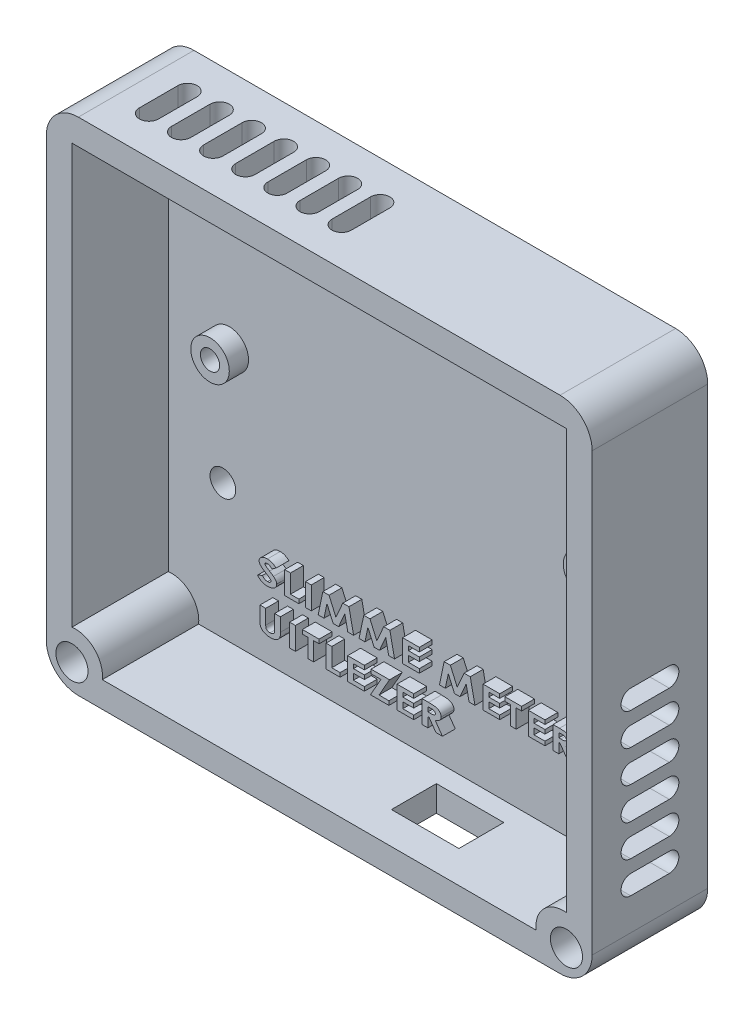
SolidWorks part; units mm, degrees
ref_plane "Front Plane" through (0, 0, 0) normal (0, 0, 1) x (1, 0, 0)
ref_plane "Top Plane" through (0, 0, 0) normal (0, 1, 0) x (1, 0, 0)
ref_plane "Right Plane" through (0, 0, 0) normal (1, 0, 0) x (0, 0, -1)
sketch "Sketch1" plane through (0, 0, 0) normal (0, 0, 1) x (1, 0, 0)
  line L0 (32.5, 30) -> (32.5, 0) construction
  line L1 (3, 0) -> (62, 0)
  line L2 (0, 3) -> (0, 27)
  line L3 (3, 30) -> (62, 30)
  line L4 (65, 3) -> (65, 27)
  line L5 (32.5, 15) -> (65, 15) construction
  line L7 (-10, 38) -> (75, 38)
  line L8 (-10, 38) -> (-10, -40)
  line L9 (-10, -40) -> (75, -40)
  line L10 (75, 38) -> (75, -40)
  circle A0 centre (3.5, 26.5) radius 1.5
  circle A1 centre (61.5, 26.5) radius 1.5
  circle A2 centre (61.5, 3.5) radius 1.5
  circle A3 centre (3.5, 3.5) radius 1.5
  arc A4 (62, 30) -> (65, 27) centre (62, 27) cw
  arc A5 (65, 3) -> (62, 0) centre (62, 3) cw
  arc A6 (3, 0) -> (0, 3) centre (3, 3) cw
  arc A7 (0, 27) -> (3, 30) centre (3, 27) cw
  point P19 (65, 30)
  point P22 (65, 0)
  point P25 (0, 0)
  point P28 (0, 30)
  dimension "D3" = 3.5
  dimension "D4" = 3
  dimension "D6" = 3
  dimension "D1" = 65
  dimension "D2" = 30
  dimension "D5" = 3.5
  dimension "D7" = 85
  dimension "D8" = 8
  dimension "D9" = 10
  dimension "D10" = 40
extrude "Base Plate" add sketch "Sketch1" along normal blind 3 contours L10 L7 L8 L9 L2 A7 L3 A4 L4 A5 L1 A6 | A7 L2 A6 L1 A5 L4 A4 L3 A1 A0 A2 A3
sketch "Sketch2" plane through (0, 0, 3) normal (0, 0, 1) x (1, 0, 0)
  line L0 (32.5, 38) -> (32.5, -40) construction
  line L1 (-10, 38) -> (75, 38) construction
  line L2 (-10, -40) -> (75, -40) construction
  circle A0 centre (3.5, 26.5) radius 1.5
  circle A1 centre (61.5, 26.5) radius 1.5
  circle A2 centre (61.5, 3.5) radius 1.5
  circle A3 centre (3.5, 3.5) radius 1.5
  circle A4 centre (3.5, 26.5) radius 3
  circle A5 centre (3.5, 3.5) radius 3
  circle A6 centre (61.5, 26.5) radius 3
  circle A7 centre (61.5, 3.5) radius 3
  dimension "D1" = 3
  dimension "D2" = 3
  dimension "D3" = 3
  dimension "D4" = 3
  dimension "D5" = 6
  dimension "D6" = 6
  dimension "D7" = 6
  dimension "D8" = 6
extrude "Pi Zero Staanders" add sketch "Sketch2" along normal blind 3
sketch "Sketch3" plane through (0, 0, 3) normal (0, 0, 1) x (1, 0, 0)
  line L1 (-10, 38) -> (75, 38)
  line L2 (-10, 38) -> (-10, -40)
  line L3 (-10, -40) -> (75, -40)
  line L4 (75, 38) -> (75, -40)
  line L5 (-6, 34) -> (71, 34)
  line L6 (-6, 34) -> (-6, -36)
  line L7 (-6, -36) -> (71, -36)
  line L8 (71, 34) -> (71, -36)
  dimension "D1" = 4
  dimension "D2" = 4
  dimension "D3" = 4
  dimension "D4" = 4
extrude "Base Walls" add sketch "Sketch3" along normal blind 15
sketch "Sketch5" plane through (0, -40, 0) normal (0, -1, 0) x (1, 0, 0)
  line L0 (-10, 0) -> (75, 0) construction
  line L1 (38.75, 13) -> (49.25, 13)
  line L2 (38.75, 13) -> (38.75, 6)
  line L3 (38.75, 6) -> (49.25, 6)
  line L4 (49.25, 13) -> (49.25, 6)
  line L6 (44, 13) -> (44, 6) construction
  line L7 (-10, 18) -> (-10, 0) construction
  dimension "D1" = 10.5
  dimension "D2" = 7
  dimension "D3" = 6
  dimension "D4" = 54
extrude "USB Power uitsnede" cut sketch "Sketch5" against normal blind 4 contours L2 L1 L4 L3
fillet "Fillet1" radius 5 1 edges at (75, 38, 9)
fillet "Fillet2" radius 5 1 edges at (-10, 38, 9)
fillet "Fillet3" radius 5 1 edges at (-10, -40, 9)
fillet "Fillet4" radius 5 1 edges at (75, -40, 9)
sketch "Sketch9" plane through (75, 0, 0) normal (1, 0, 0) x (0, 0, -1)
  line L0 (-9, -40) -> (-9, 38) construction
  line L1 (0, -40) -> (-18, -40) construction
  line L2 (-18, 38) -> (0, 38) construction
  line L3 (-12, -28.5) -> (-6, -28.5) construction
  line L4 (-12, -27) -> (-6, -27)
  line L5 (-12, -30) -> (-6, -30)
  line L6 (-18, -35) -> (-18, 33) construction
  line L9 (-12, -23.5) -> (-6, -23.5) construction
  line L12 (-12, -22) -> (-6, -22)
  line L15 (-12, -25) -> (-6, -25)
  line L18 (-12, -18.5) -> (-6, -18.5) construction
  line L19 (-12, -17) -> (-6, -17)
  line L20 (-12, -20) -> (-6, -20)
  line L21 (-12, -13.5) -> (-6, -13.5) construction
  line L22 (-12, -12) -> (-6, -12)
  line L23 (-12, -15) -> (-6, -15)
  line L24 (-12, -8.5) -> (-6, -8.5) construction
  line L25 (-12, -7) -> (-6, -7)
  line L26 (-12, -10) -> (-6, -10)
  line L27 (-12, -3.5) -> (-6, -3.5) construction
  line L28 (-12, -2) -> (-6, -2)
  line L29 (-12, -5) -> (-6, -5)
  arc A0 (-12, -27) -> (-12, -30) centre (-12, -28.5) ccw
  arc A1 (-6, -30) -> (-6, -27) centre (-6, -28.5) ccw
  arc A10 (-12, -22) -> (-12, -25) centre (-12, -23.5) ccw
  arc A11 (-6, -25) -> (-6, -22) centre (-6, -23.5) ccw
  arc A12 (-12, -17) -> (-12, -20) centre (-12, -18.5) ccw
  arc A13 (-6, -20) -> (-6, -17) centre (-6, -18.5) ccw
  arc A14 (-12, -12) -> (-12, -15) centre (-12, -13.5) ccw
  arc A15 (-6, -15) -> (-6, -12) centre (-6, -13.5) ccw
  arc A16 (-12, -7) -> (-12, -10) centre (-12, -8.5) ccw
  arc A17 (-6, -10) -> (-6, -7) centre (-6, -8.5) ccw
  arc A18 (-12, -2) -> (-12, -5) centre (-12, -3.5) ccw
  arc A19 (-6, -5) -> (-6, -2) centre (-6, -3.5) ccw
  point P8 (-9, -28.5)
  point P18 (-9, -23.5)
  point P25 (-9, -18.5)
  point P32 (-9, -13.5)
  point P39 (-9, -8.5)
  point P46 (-9, -3.5)
  dimension "D3" = 9
  dimension "D1" = 3
  dimension "D2" = 10
  dimension "D5" = 6
  dimension "D4" = 6
extrude "Lucht ventilatie Rechts" cut sketch "Sketch9" against normal blind 4 contours L25 A17 L26 A16 | L22 A15 L23 A14 | L19 A13 L20 A12 | L12 A11 L15 A10 | L5 A1 L4 A0 | L28 A19 L29 A18
sketch "Sketch10" plane through (0, 0, 3) normal (0, 0, 1) x (1, 0, 0)
  line L0 (32.5, 38) -> (32.5, -40) construction
  line L1 (70, 38) -> (-5, 38) construction
  line L2 (-5, -40) -> (70, -40) construction
  line L3 (32.5, -1) -> (-10, -1) construction
  line L4 (-10, 33) -> (-10, -35) construction
  circle A0 centre (2.5, -15.0716) radius 2
  circle A1 centre (62.5, -15.0716) radius 2
  dimension "D2" = 4
  dimension "D3" = 4
  dimension "D4" = 30
  dimension "D5" = 30
extrude "Holes for screw" cut sketch "Sketch10" against normal through all
sketch "Sketch11" plane through (0, 38, 0) normal (0, 1, 0) x (1, 0, 0)
  line L0 (-10, -9) -> (75, -9) construction
  line L1 (-10, -18) -> (-10, 0) construction
  line L2 (75, 0) -> (75, -18) construction
  line L3 (0, -12) -> (0, -6) construction
  line L4 (-1.5, -12) -> (-1.5, -6)
  line L5 (1.5, -12) -> (1.5, -6)
  line L6 (6.5, -12) -> (6.5, -6)
  line L9 (3.5, -12) -> (3.5, -6)
  line L12 (5, -12) -> (5, -6) construction
  line L15 (11.5, -12) -> (11.5, -6)
  line L18 (8.5, -12) -> (8.5, -6)
  line L21 (10, -12) -> (10, -6) construction
  line L24 (16.5, -12) -> (16.5, -6)
  line L27 (13.5, -12) -> (13.5, -6)
  line L30 (15, -12) -> (15, -6) construction
  line L33 (21.5, -12) -> (21.5, -6)
  line L36 (18.5, -12) -> (18.5, -6)
  line L39 (20, -12) -> (20, -6) construction
  line L42 (26.5, -12) -> (26.5, -6)
  line L45 (23.5, -12) -> (23.5, -6)
  line L48 (25, -12) -> (25, -6) construction
  line L49 (31.5, -12) -> (31.5, -6)
  line L50 (28.5, -12) -> (28.5, -6)
  line L51 (30, -12) -> (30, -6) construction
  arc A0 (-1.5, -12) -> (1.5, -12) centre (0, -12) ccw
  arc A1 (1.5, -6) -> (-1.5, -6) centre (0, -6) ccw
  arc A30 (3.5, -12) -> (6.5, -12) centre (5, -12) ccw
  arc A31 (6.5, -6) -> (3.5, -6) centre (5, -6) ccw
  arc A32 (8.5, -12) -> (11.5, -12) centre (10, -12) ccw
  arc A33 (11.5, -6) -> (8.5, -6) centre (10, -6) ccw
  arc A34 (13.5, -12) -> (16.5, -12) centre (15, -12) ccw
  arc A35 (16.5, -6) -> (13.5, -6) centre (15, -6) ccw
  arc A36 (18.5, -12) -> (21.5, -12) centre (20, -12) ccw
  arc A37 (21.5, -6) -> (18.5, -6) centre (20, -6) ccw
  arc A38 (23.5, -12) -> (26.5, -12) centre (25, -12) ccw
  arc A39 (26.5, -6) -> (23.5, -6) centre (25, -6) ccw
  arc A40 (28.5, -12) -> (31.5, -12) centre (30, -12) ccw
  arc A41 (31.5, -6) -> (28.5, -6) centre (30, -6) ccw
  point P8 (0, -9)
  point P17 (5, -9)
  point P24 (10, -9)
  point P31 (15, -9)
  point P38 (20, -9)
  point P45 (25, -9)
  point P52 (30, -9)
  dimension "D2" = 6
  dimension "D1" = 3
  dimension "D3" = 10
  dimension "D4" = 7
extrude "Cool holes" cut sketch "Sketch11" against normal blind 4
sketch "Sketch15" plane through (0, 0, 3) normal (0, 0, 1) x (1, 0, 0)
  line L0 (-10, 33) -> (-10, -35) construction
  line L1 (-5, -40) -> (70, -40) construction
  line L2 (32.5, 38) -> (32.5, -40) construction
  line L4 (70, 38) -> (-5, 38) construction
  circle A0 centre (-5.5, -35.5) radius 4.25
  circle A2 centre (-5.5, -35.5) radius 1.475
  circle A3 centre (70.5, -35.5) radius 1.475
  circle A4 centre (70.5, -35.5) radius 4.25
  dimension "D3" = 8.5
  dimension "D4" = 2.95
  dimension "D1" = 4.5
  dimension "D2" = 4.5
extrude "Screw Holes" add sketch "Sketch15" along normal through all contours A0 | A2 | A4 | A3
sketch "Sketch17" plane through (0, 0, 3) normal (0, 0, 1) x (1, 0, 0)
  text T0 "<b>SLIMME METER</b>\r\n<b>UITLEZER</b>" font "Century Gothic" height 3.5
extrude "Tekst" add sketch "Sketch17" along normal blind 2
sketch "Sketch18" plane through (0, 34, 0) normal (0, -1, 0) x (1, 0, 0)
  line L0 (32.5, 18) -> (32.5, 3) construction
  line L1 (71, 18) -> (-6, 18) construction
  line L2 (71, 3) -> (-6, 3) construction
  line L3 (32.5, 18) -> (52.5, 18) construction
  line L8 (52.5, 18) -> (52.5, 11.5) construction
  line L10 (45, 14.5) -> (60, 14.5)
  line L11 (45, 14.5) -> (45, 17)
  line L12 (45, 17) -> (60, 17)
  line L13 (60, 14.5) -> (60, 17)
  line L14 (45, 14.5) -> (60, 17) construction
  line L15 (45, 17) -> (60, 14.5) construction
  point P6 (52.5, 15.75)
  dimension "D1" = 15
  dimension "D2" = 1
  dimension "D3" = 2.5
  dimension "D4" = 20
  dimension "D5" = 8.5
extrude "Cut-Extrude1" cut sketch "Sketch18" against normal blind 2.5
sketch "Sketch19" plane through (0, 0, 18) normal (0, 0, 1) x (1, 0, 0)
  circle A0 centre (71, -36) radius 2.5
  circle A1 centre (-6, -36) radius 2.5
  dimension "D1" = 5
  dimension "D2" = 5
extrude "Cut-Extrude2" cut sketch "Sketch19" against normal blind 16 contours A0 | A1
